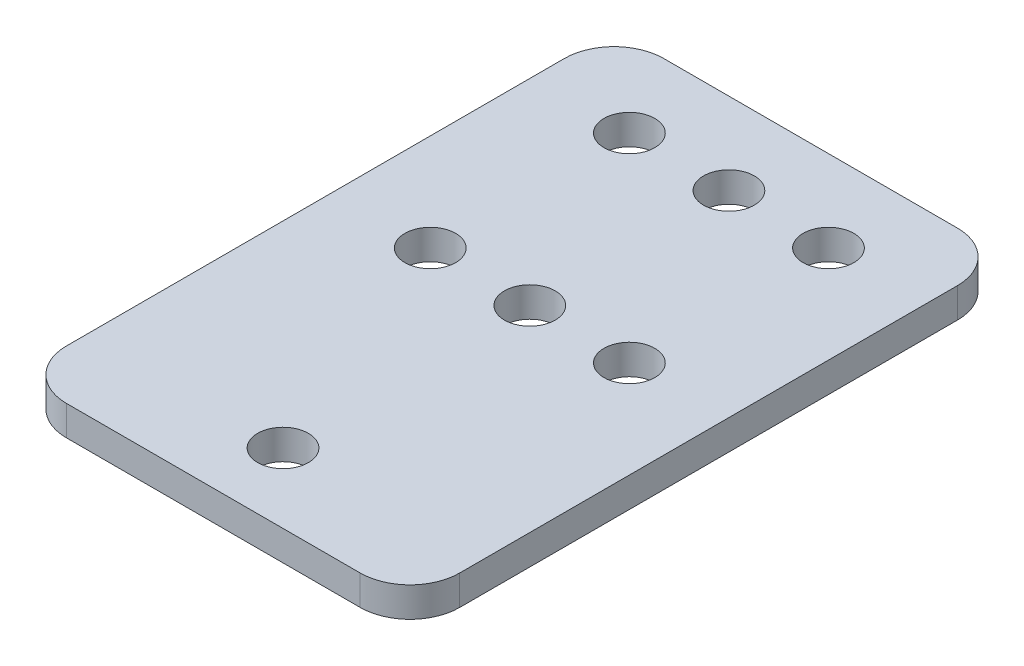
SolidWorks part; units mm, degrees
ref_plane "Front Plane" through (0, 0, 0) normal (0, 0, 1) x (1, 0, 0)
ref_plane "Top Plane" through (0, 0, 0) normal (0, 1, 0) x (1, 0, 0)
ref_plane "Right Plane" through (0, 0, 0) normal (1, 0, 0) x (0, 0, -1)
sketch "Sketch1" plane through (0, 0, 0) normal (0, 1, 0) x (1, 0, 0)
  line L1 (-19.75, -30) -> (19.75, -30)
  line L2 (-19.75, -30) -> (-19.75, 30)
  line L3 (-19.75, 30) -> (19.75, 30)
  line L4 (19.75, -30) -> (19.75, 30)
  line L5 (-19.75, -30) -> (19.75, 30) construction
  line L6 (-19.75, 30) -> (19.75, -30) construction
  point P0 (0, 0)
  point P6 (0, 0)
  point P8 (0, 0)
  dimension "D1" = 60
  dimension "D2" = 39.5
  dimension "D3" = 0
extrude "Boss-Extrude1" add sketch "Sketch1" along normal blind 3
sketch "Sketch2" plane through (0, 3, 0) normal (0, 1, 0) x (1, 0, 0)
  line L0 (0, -1.65) -> (0, 1.65) construction
  line L1 (19.75, 30) -> (-19.75, 30) construction
  circle A0 centre (0, 21.79) radius 2.55
  dimension "D2" = 5.1
  dimension "D1" = 8.21
extrude "Cut-Extrude1" cut sketch "Sketch2" against normal through all
sketch "Sketch4" plane through (0, 3, 0) normal (0, 1, 0) x (1, 0, 0)
  line L0 (0, -1.65) -> (0, 1.65) construction
  line L1 (-19.75, -30) -> (19.75, -30) construction
  circle A0 centre (0, -23) radius 2.55
  dimension "D2" = 5.1
  dimension "D1" = 7
extrude "Cut-Extrude2" cut sketch "Sketch4" against normal through all
pattern_linear "LPattern1" count 2 spacing 10 along (-1, 0, 0) count 2 spacing 10 along (1, 0, 0) of "Cut-Extrude1"
pattern_linear "LPattern2" count 2 spacing 20 along (0, 0, 1) of "LPattern1", "Cut-Extrude1"
fillet "Fillet1" radius 5 1 edges at (-19.75, 1.5, 30)
fillet "Fillet2" radius 5 1 edges at (19.75, 1.5, -30)
fillet "Fillet3" radius 5 1 edges at (19.75, 1.5, 30)
fillet "Fillet4" radius 5 1 edges at (-19.75, 1.5, -30)
